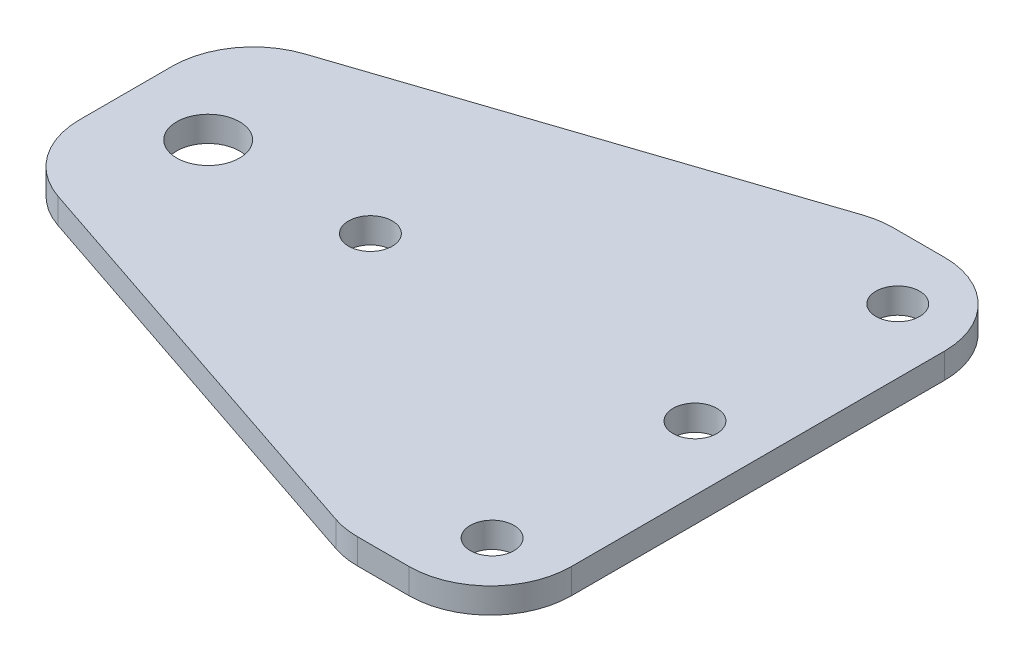
SolidWorks part; units mm, degrees
ref_plane "Front Plane" through (0, 0, 0) normal (0, 0, 1) x (1, 0, 0)
ref_plane "Top Plane" through (0, 0, 0) normal (0, 1, 0) x (1, 0, 0)
ref_plane "Right Plane" through (0, 0, 0) normal (1, 0, 0) x (0, 0, -1)
sketch "Sketch1" plane through (0, 0, 0) normal (0, 1, 0) x (1, 0, 0)
  line L0 (0, 25.8102) -> (0, 0)
  line L1 (0, 25.8102) -> (60, 45.8102)
  line L2 (0, 0) -> (60, -20.1898)
  line L3 (60, 45.8102) -> (78, 45.8102)
  line L4 (78, 45.8102) -> (78, -20.1898)
  line L5 (78, -20.1898) -> (60, -20.1898)
  circle A0 centre (70.0741, -12.0339) radius 2.7
  circle A1 centre (10.0741, 12.9661) radius 3.875
  circle A2 centre (70.0741, 37.9661) radius 2.7
  circle A3 centre (70.0741, 12.9661) radius 2.7
  circle A4 centre (30.0741, 12.9661) radius 2.7
  dimension "D2" = 5.4
  dimension "D3" = 7.75
  dimension "D11" = 7.9259
  dimension "D12" = 7.8441
  dimension "D13" = 25
  dimension "D14" = 25
  dimension "D15" = 40
  dimension "D1" = 60
  dimension "D4" = 60
  dimension "D5" = 20
  dimension "D6" = 50
  dimension "D7" = 63.3058
  dimension "D8" = 18
  dimension "D9" = 18
  dimension "D10" = 25.8102
extrude "Boss-Extrude1" add sketch "Sketch1" along normal blind 3.125
fillet "Fillet1" radius 10 6 edges at (78, 1.5625, -45.8102) (78, 1.5625, 20.1898) (60, 1.5625, 20.1898) (60, 1.5625, -45.8102) (0, 1.5625, -25.8102) (0, 1.5625, 0)
